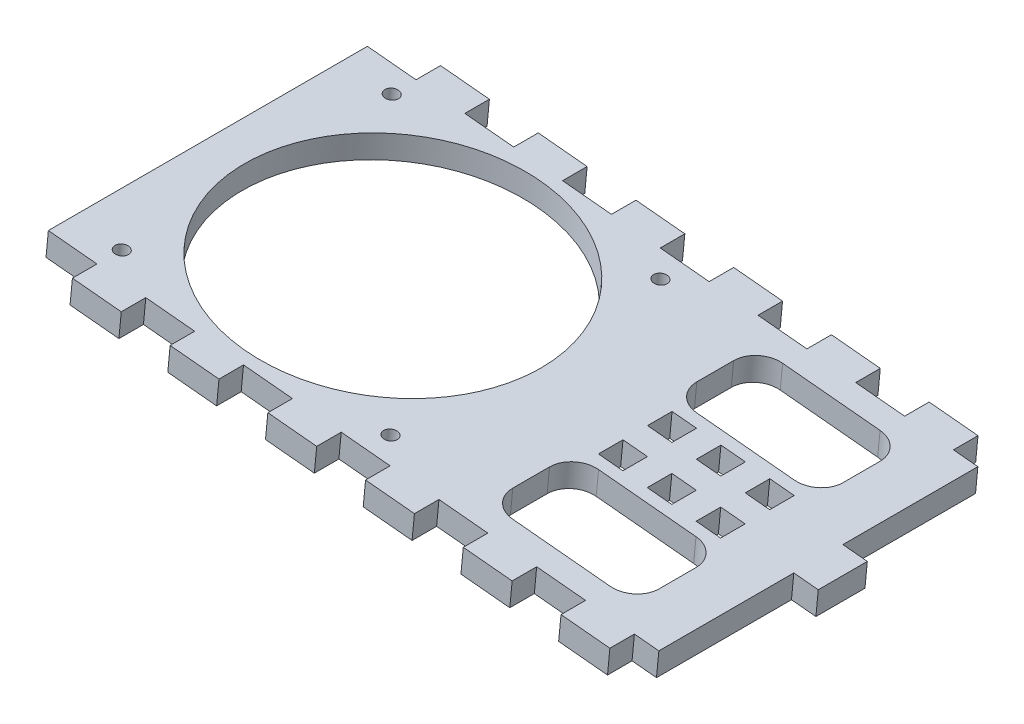
SolidWorks part; units mm, degrees
ref_plane "Front Plane" through (0, 0, 0) normal (0, 0, 1) x (1, 0, 0)
ref_plane "Top Plane" through (0, 0, 0) normal (0, 1, 0) x (1, 0, 0)
ref_plane "Right Plane" through (0, 0, 0) normal (1, 0, 0) x (0, 0, -1)
sketch "Sketch1" plane through (0, 0, 0) normal (0, 0, 1) x (1, 0, 0)
  line L0 (0, 0) -> (40.3547, 419.1) construction
  line L1 (40.3547, 419.1) -> (159.2585, 419.1) construction
  line L2 (159.2585, 419.1) -> (159.2585, 0) construction
  line L3 (159.2585, 0) -> (0, 0) construction
  line L4 (159.2585, -1000) -> (159.2585, 49000) construction
  line L5 (2.0164, 20.9415) -> (40.3547, 419.1) construction
  line L6 (2.0164, 20.9415) -> (41.8323, 17.1077) construction
  line L7 (40.3547, 419.1) -> (80.1706, 415.2662) construction
  line L8 (41.8323, 17.1077) -> (80.1706, 415.2662) construction
  line L9 (64.0085, -1000) -> (64.0085, 49000) construction
  line L10 (-42.7214, 317.5) -> (-118.5706, 324.8034) construction
  line L11 (-20.0013, 414.3375) -> (40.196, 414.3375) construction
  line L12 (-1162.1335, 304.8) -> (48837.8665, 304.8) construction
  line L13 (-120.1415, 292.1) -> (-43.9415, 292.1) construction
  line L14 (-118.5706, 324.8034) -> (-43.9415, 292.1) construction
  line L15 (-42.7214, 317.5) -> (-120.1415, 292.1) construction
  line L16 (40.196, 338.1375) -> (-20.0013, 338.1375) construction
  line L17 (-128.0517, 325.7164) -> (29.8985, 310.5075)
  line L18 (-128.0517, 325.7164) -> (-127.4431, 332.0371)
  line L19 (-127.4431, 332.0371) -> (40.3547, 419.1)
  line L20 (40.3547, 419.1) -> (108.4585, 419.1)
  line L21 (108.4585, 419.1) -> (108.4585, 0) construction
  line L22 (29.8985, 310.5075) -> (0.4102, 4.2603)
  line L23 (0.4102, 4.2603) -> (44.6556, 0)
  line L24 (44.6556, 0) -> (108.4585, 0)
  line L25 (108.4585, 419.1) -> (159.2585, 311.15)
  line L26 (159.2585, 311.15) -> (159.2585, 304.8)
  line L27 (159.2585, 304.8) -> (108.4585, 280.8941)
  line L28 (108.4585, 280.8941) -> (108.4585, 0)
  arc A0 (-118.5706, 324.8034) -> (-20.0013, 414.3375) centre (-20.0013, 315.3123) cw construction
  arc A1 (73.5335, 304.8) -> (40.196, 338.1375) centre (40.196, 304.8) ccw construction
  arc A2 (149.7335, 304.8) -> (40.196, 414.3375) centre (40.196, 304.8) ccw construction
  arc A3 (-42.7214, 317.5) -> (-20.0013, 338.1375) centre (-20.0013, 315.3123) cw construction
  point P7 (57.6585, 400.05)
  point P17 (149.7335, 304.8)
  point P18 (73.5335, 304.8)
  dimension "D9" = 9.525
  dimension "D14" = 25.4
  dimension "D1" = 419.1
  dimension "D2" = 101.6
  dimension "D3" = 19.05
  dimension "D4" = 19.05
  dimension "D5" = 84.5
  dimension "D6" = 40
  dimension "D7" = 400
  dimension "D8" = 95.25
  dimension "D10" = 9.525
  dimension "D11" = 114.3
  dimension "D12" = 76.2
  dimension "D13" = 9.525
  dimension "D15" = 127
  dimension "D16" = 9.525
  dimension "D17" = 203.2
  dimension "D18" = 6.35
  dimension "D19" = 50.8
  dimension "D20" = 44.45
  dimension "D21" = 6.35
sketch "Sketch2" plane through (0, 0, 0) normal (0, 0, 1) x (1, 0, 0)
  line L0 (-127.4431, 332.0371) -> (-128.0517, 325.7164)
  line L1 (-127.4431, 332.0371) -> (36.8279, 316.2196)
  line L2 (-128.0517, 325.7164) -> (36.2192, 309.8989)
  line L3 (36.8279, 316.2196) -> (36.2192, 309.8989)
  line L8 (29.8985, 310.5075) -> (0.4102, 4.2603) construction
  dimension "D1" = 6.35
extrude "Boss-Extrude1" add sketch "Sketch2" along normal blind 95.25
sketch "Sketch3" plane through (30.5071, 316.8283, 0) normal (0.0958, 0.9954, 0) x (0.9954, -0.0958, 0)
  line L0 (-111.0558, -47.625) -> (-111.0558, 0) construction
  line L1 (-149.1558, 0) -> (-72.9558, 0) construction
  line L2 (-158.6808, -47.625) -> (-111.0558, -47.625) construction
  line L3 (-158.6808, -95.25) -> (-158.6808, 0) construction
  line L4 (6.35, 0) -> (-158.6808, 0) construction
  line L7 (-72.0547, -47.625) -> (-72.0547, 0) construction
  line L8 (-149.1558, 0) -> (-149.1558, -47.625) construction
  ellipse E0 centre (-110.6052, -47.625) end of major axis (-72.0547, -47.625) minor radius 38.1
  point P6 (-72.0547, 0)
  dimension "D1" = 76.2
extrude "Cut-Extrude1" cut sketch "Sketch3" against normal through all
sketch "Sketch4" plane through (30.5071, 316.8283, 0) normal (0.0958, 0.9954, 0) x (0.9954, -0.0958, 0)
  line L0 (-158.6808, -95.25) -> (-158.6808, 0) construction
  line L1 (-76.1308, -82.55) -> (-145.9808, -82.55) construction
  line L2 (-76.1308, -82.55) -> (-76.1308, -12.7) construction
  line L3 (-76.1308, -12.7) -> (-145.9808, -12.7) construction
  line L4 (-145.9808, -82.55) -> (-145.9808, -12.7) construction
  line L5 (-76.1308, -82.55) -> (-145.9808, -12.7) construction
  line L6 (-76.1308, -12.7) -> (-145.9808, -82.55) construction
  circle A0 centre (-145.9808, -12.7) radius 1.75
  circle A1 centre (-145.9808, -82.55) radius 1.75
  circle A2 centre (-76.1308, -82.55) radius 1.75
  circle A3 centre (-76.1308, -12.7) radius 1.75
  point P0 (-111.0558, -47.625)
  dimension "D2" = 3.5
  dimension "D1" = 69.85
  dimension "D3" = 47.625
extrude "Cut-Extrude2" cut sketch "Sketch4" against normal through all
sketch "Sketch5" plane through (30.5071, 316.8283, 0) normal (0.0958, 0.9954, 0) x (0.9954, -0.0958, 0)
  line L0 (-158.6808, -95.25) -> (-158.6808, 0) construction
  line L1 (-50.7308, -12.7) -> (-12.7, -12.7)
  line L2 (-50.7308, -12.7) -> (-50.7308, -82.55)
  line L3 (-50.7308, -82.55) -> (-12.7, -82.55)
  line L4 (-12.7, -12.7) -> (-12.7, -82.55)
  line L5 (6.35, -95.25) -> (-158.6808, -95.25) construction
  line L6 (-147.5849, 0) -> (-71.7357, 0) construction
  point P10 (0, 0)
  dimension "D1" = 107.95
  dimension "D2" = 12.7
  dimension "D3" = 12.7
  dimension "D4" = 12.7
extrude "Cut-Extrude3" cut sketch "Sketch5" against normal through all
sketch "Sketch7" plane through (30.5071, 316.8283, 0) normal (0.0958, 0.9954, 0) x (0.9954, -0.0958, 0)
  line L1 (6.35, 0) -> (-6.35, 0)
  line L2 (6.35, 0) -> (6.35, -6.35)
  line L3 (6.35, -6.35) -> (-6.35, -6.35)
  line L4 (-6.35, 0) -> (-6.35, -6.35)
  line L5 (6.35, -95.25) -> (-6.35, -95.25)
  line L6 (6.35, -95.25) -> (6.35, -88.9)
  line L7 (6.35, -88.9) -> (-6.35, -88.9)
  line L8 (-6.35, -95.25) -> (-6.35, -88.9)
  dimension "D1" = 6.35
  dimension "D2" = 12.7
extrude "Cut-Extrude4" cut sketch "Sketch7" against normal through all
pattern_linear "LPattern1" count 17 spacing 25.4 along (-0.9954, 0.0958, 0) of "Cut-Extrude4"
sketch "Sketch8" plane through (30.5071, 316.8283, 0) normal (0.0958, 0.9954, 0) x (0.9954, -0.0958, 0)
  line L1 (0, -6.35) -> (6.35, -6.35)
  line L2 (0, -6.35) -> (0, -41.275)
  line L3 (0, -41.275) -> (6.35, -41.275)
  line L4 (6.35, -6.35) -> (6.35, -41.275)
  line L5 (0, -88.9) -> (6.35, -88.9)
  line L6 (0, -88.9) -> (0, -53.975)
  line L7 (0, -53.975) -> (6.35, -53.975)
  line L8 (6.35, -88.9) -> (6.35, -53.975)
  dimension "D1" = 12.7
  dimension "D2" = 6.35
extrude "Cut-Extrude5" cut sketch "Sketch8" against normal through all
sketch "Sketch9" plane through (30.5071, 316.8283, 0) normal (0.0958, 0.9954, 0) x (0.9954, -0.0958, 0)
  line L0 (-50.7308, -12.7) -> (-12.7, -82.55) construction
  line L1 (-12.7, -82.55) -> (-12.7, -12.7) construction
  line L2 (-50.7308, -60.325) -> (-12.7, -60.325)
  line L3 (-50.7308, -60.325) -> (-50.7308, -34.925)
  line L4 (-50.7308, -34.925) -> (-12.7, -34.925)
  line L5 (-12.7, -60.325) -> (-12.7, -34.925)
  line L6 (-50.7308, -60.325) -> (-12.7, -34.925) construction
  line L7 (-50.7308, -34.925) -> (-12.7, -60.325) construction
  point P4 (-31.7154, -47.625)
  dimension "D1" = 25.4
extrude "Boss-Extrude2" add sketch "Sketch9" against normal blind 6.35
sketch "Sketch10" plane through (30.5071, 316.8283, 0) normal (0.0958, 0.9954, 0) x (0.9954, -0.0958, 0)
  line L0 (-31.7154, -34.925) -> (-31.7154, -60.325) construction
  line L1 (-12.7, -34.925) -> (-50.7308, -34.925) construction
  line L2 (-50.7308, -60.325) -> (-12.7, -60.325) construction
  line L4 (-34.8904, -44.45) -> (-28.5404, -44.45)
  line L5 (-34.8904, -44.45) -> (-34.8904, -38.1)
  line L6 (-34.8904, -38.1) -> (-28.5404, -38.1)
  line L7 (-28.5404, -44.45) -> (-28.5404, -38.1)
  line L8 (-34.8904, -44.45) -> (-28.5404, -38.1) construction
  line L9 (-34.8904, -38.1) -> (-28.5404, -44.45) construction
  line L10 (-34.8904, -57.15) -> (-28.5404, -57.15)
  line L11 (-34.8904, -57.15) -> (-34.8904, -50.8)
  line L12 (-34.8904, -50.8) -> (-28.5404, -50.8)
  line L13 (-28.5404, -57.15) -> (-28.5404, -50.8)
  line L14 (-34.8904, -57.15) -> (-28.5404, -50.8) construction
  line L15 (-34.8904, -50.8) -> (-28.5404, -57.15) construction
  point P8 (-31.7154, -41.275)
  point P13 (-31.7154, -53.975)
  dimension "D1" = 6.35
  dimension "D2" = 3.175
  dimension "D3" = 3.175
extrude "Cut-Extrude6" cut sketch "Sketch10" against normal through all
pattern_linear "LPattern2" count 2 spacing 12.7 along (0.9954, -0.0958, 0) count 2 spacing 12.7 along (-0.9954, 0.0958, 0) of "Cut-Extrude6"
fillet "Fillet1" radius 6.35 8 edges at (-20.2944, 318.5302, 82.55) (17.5613, 314.8851, 60.325) (17.5613, 314.8851, 82.55) (17.5613, 314.8851, 34.925) (17.5613, 314.8851, 12.7) (-20.2944, 318.5302, 12.7) (-20.2944, 318.5302, 34.925) (-20.2944, 318.5302, 60.325)
